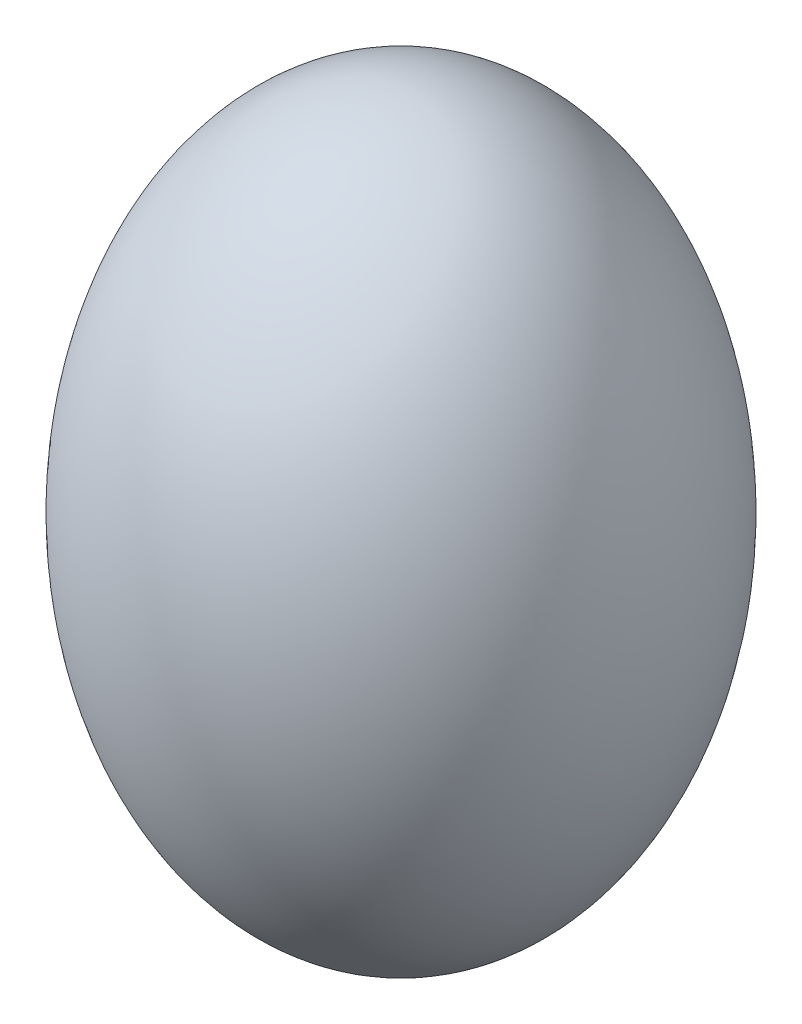
SolidWorks part; units mm, degrees
ref_plane "Front Plane" through (0, 0, 0) normal (0, 0, 1) x (1, 0, 0)
ref_plane "Top Plane" through (0, 0, 0) normal (0, 1, 0) x (1, 0, 0)
ref_plane "Right Plane" through (0, 0, 0) normal (1, 0, 0) x (0, 0, -1)
sketch "Sketch1" plane through (0, 0, 0) normal (0, 0, 1) x (1, 0, 0)
  line L0 (0, 80.2354) -> (0, -83.657) construction
  line L1 (0, 32.5) -> (0, -32.5)
  ellipse E0 centre (0, 0) end of major axis (0, 32.5) minor radius 22.5 (0, 32.5) -> (0, -32.5) ccw
  dimension "D1" = 65
  dimension "D2" = 45
revolve "Revolve1" add sketch "Sketch1" angle 360 about L0
